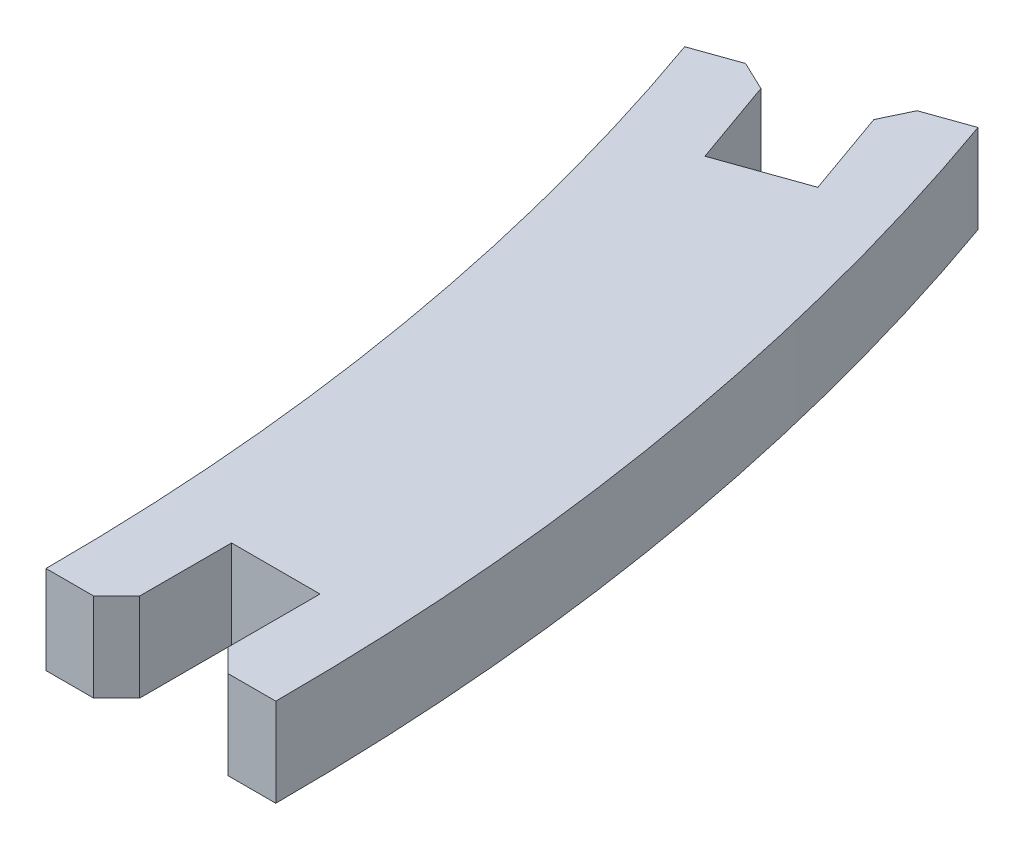
SolidWorks part; units mm, degrees
ref_plane "Front" through (0, 0, 0) normal (0, 0, 1) x (1, 0, 0)
ref_plane "Top" through (0, 0, 0) normal (0, 1, 0) x (1, 0, 0)
ref_plane "Right" through (0, 0, 0) normal (1, 0, 0) x (0, 0, -1)
sketch "Sketch1" plane through (0, 0, 0) normal (0, 1, 0) x (1, 0, 0)
  line L0 (-11.1163, 35.7085) -> (-123.1921, -3.9796) construction
  line L1 (-17.6441, 33.3969) -> (-14.7455, 34.4233)
  line L4 (-13.3267, 36.1837) -> (-11.2332, 30.2718) construction
  line L5 (-11.1163, 35.7085) -> (-9.4473, 30.9953)
  line L6 (-6.877, 22.6701) -> (-6.877, 6.6231) construction
  line L7 (-14.7455, 34.4233) -> (-13.0764, 29.7101)
  line L8 (-9.4473, 30.9953) -> (-13.0764, 29.7101)
  line L9 (-11.1163, 35.7085) -> (-8.2177, 36.735)
  line L10 (-11.877, -0.1658) -> (-8.802, -0.1658)
  line L11 (-4.952, -0.1658) -> (-4.952, 4.8342)
  line L12 (-4.952, 4.8342) -> (-8.802, 4.8342)
  line L13 (-8.802, -0.1658) -> (-8.802, 4.8342)
  line L14 (-4.952, -0.1658) -> (-1.877, -0.1658)
  line L15 (48.8632, -0.1658) -> (-176.8655, -0.1658) construction
  circle A0 centre (-112.4222, -0.1658) radius 110.5452 construction
  circle A1 centre (-112.4222, -0.1658) radius 100.5452 construction
  circle A2 centre (-112.4222, -0.1658) radius 105.5452 construction
  arc A3 (-11.877, -0.1658) -> (-17.6441, 33.3969) centre (-112.4222, -0.1658) ccw
  arc A4 (-1.877, -0.1658) -> (-8.2177, 36.735) centre (-112.4222, -0.1658) ccw
  point P27 (-148.786, -0.1658)
  dimension "D6" = 211.0905
  dimension "D2" = 3.85
  dimension "D3" = 5
  dimension "D4" = 5
  dimension "D5" = 3.85
  dimension "D1" = 160.5
  dimension "D7" = 5
extrude "Boss-Extrude1" add sketch "Sketch1" along normal blind 3.85 contours L13 L12 L11 L14 A4 L9 L5 L8 L7 L1 A3 L10
chamfer "Chamfer1" distance 1 angle 45 4 edges at (-8.802, 1.925, 0.1658) (-4.952, 1.925, 0.1658) (-14.7455, 1.925, -34.4233) (-11.1163, 1.925, -35.7085)
equation "\"entrance\"=5"
equation "\"D1@Boss-Extrude1\" = \"thick\""
equation "\"D2@Sketch1\" = \"thick\""
equation "\"D5@Sketch1\"= \"thick\""
equation "\"D4@Sketch1\"=\"entrance\""
equation "\"D3@Sketch1\"=\"entrance\""
equation "\"thick\"=3.85"
